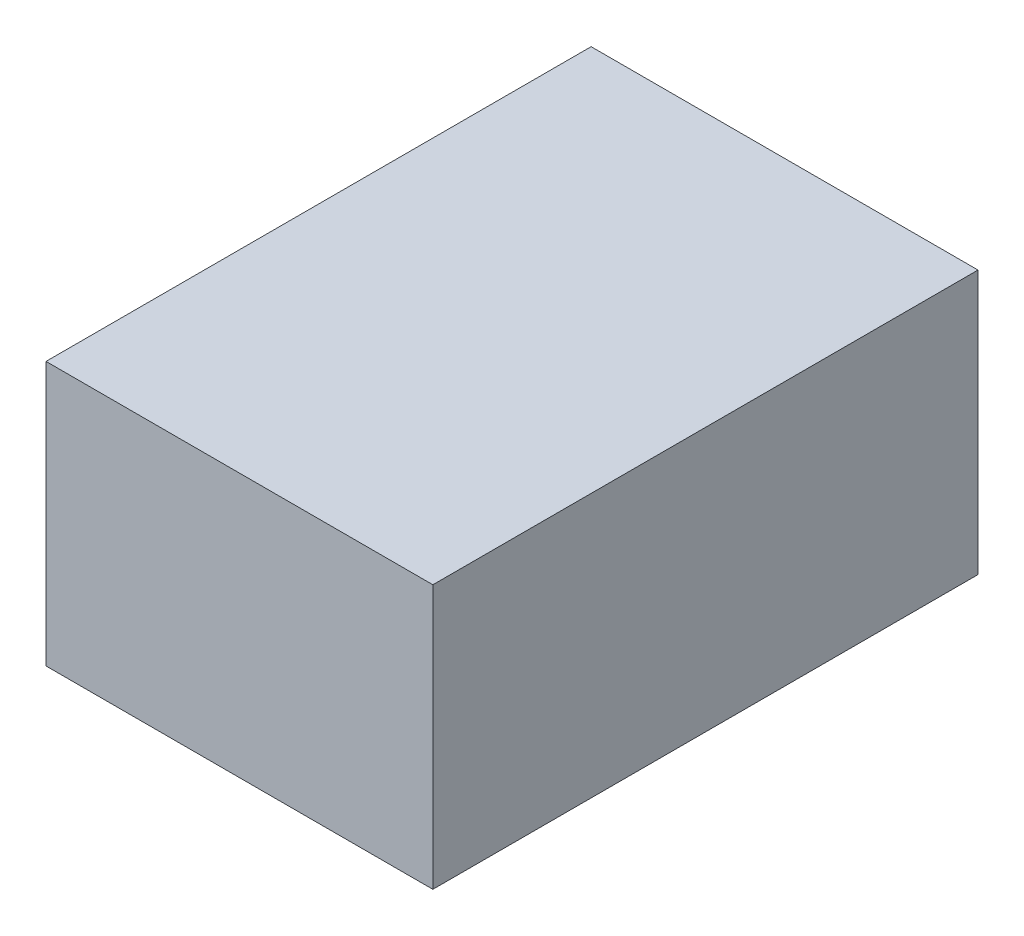
SolidWorks part; units mm, degrees
ref_plane "Plan de face" through (0, 0, 0) normal (0, 0, 1) x (1, 0, 0)
ref_plane "Plan de dessus" through (0, 0, 0) normal (0, 1, 0) x (1, 0, 0)
ref_plane "Plan de droite" through (0, 0, 0) normal (1, 0, 0) x (0, 0, -1)
sketch "Esquisse1" plane through (0, 0, 0) normal (0, 1, 0) x (1, 0, 0)
  line L1 (22, 31) -> (-22, 31)
  line L2 (22, 31) -> (22, -31)
  line L3 (22, -31) -> (-22, -31)
  line L4 (-22, 31) -> (-22, -31)
  line L5 (22, 31) -> (-22, -31) construction
  line L6 (22, -31) -> (-22, 31) construction
  point P0 (0, 0)
  dimension "D1" = 44
extrude "Boss.-Extru.1" add sketch "Esquisse1" along normal blind 30
